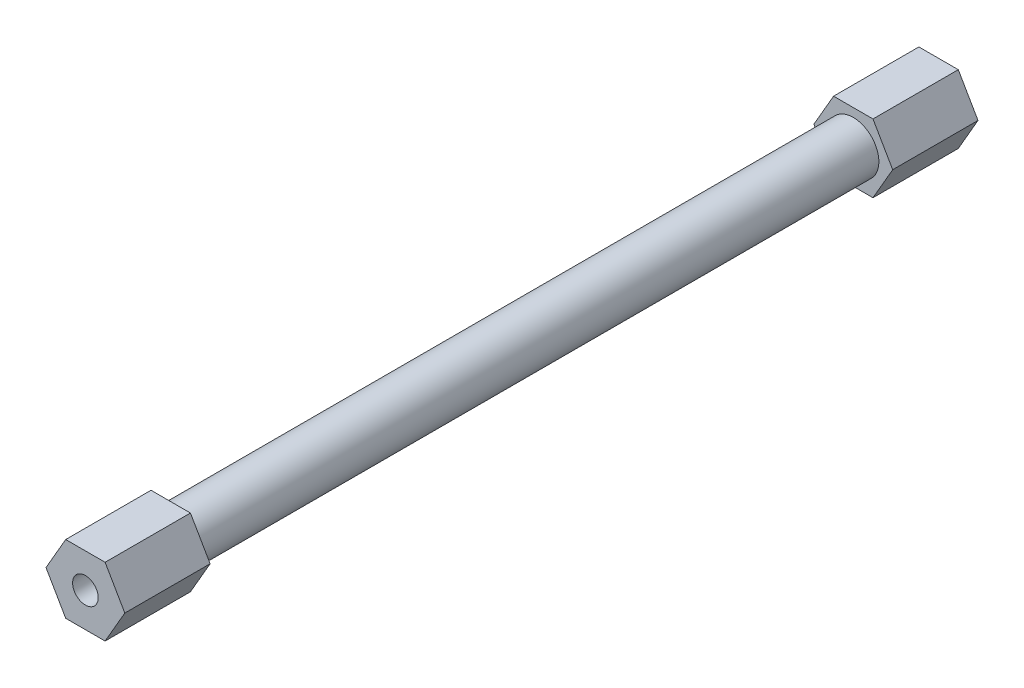
SolidWorks part; units mm, degrees
material "1060 Alloy"
ref_plane "Front Plane" through (0, 0, 0) normal (0, 0, 1) x (1, 0, 0)
ref_plane "Top Plane" through (0, 0, 0) normal (0, 1, 0) x (1, 0, 0)
ref_plane "Right Plane" through (0, 0, 0) normal (1, 0, 0) x (0, 0, -1)
sketch "Sketch1" plane through (0, 0, 0) normal (0, 0, 1) x (1, 0, 0)
  circle A0 centre (0, 0) radius 1.5
  circle A1 centre (0, 0) radius 3
  dimension "D1" = 3
  dimension "D2" = 6
extrude "Boss-Extrude1" add sketch "Sketch1" along normal blind 100
sketch "Sketch2" plane through (0, 0, 100) normal (0, 0, 1) x (1, 0, 0)
  line L1 (4.6188, 0) -> (2.3094, 4)
  line L2 (2.3094, 4) -> (-2.3094, 4)
  line L3 (-2.3094, 4) -> (-4.6188, 0)
  line L4 (-4.6188, 0) -> (-2.3094, -4)
  line L5 (-2.3094, -4) -> (2.3094, -4)
  line L6 (2.3094, -4) -> (4.6188, 0)
  circle A0 centre (0, 0) radius 4 construction
  circle A1 centre (0, 0) radius 1.5
  dimension "D1" = 8
extrude "Boss-Extrude2" add sketch "Sketch2" against normal blind 10
ref_plane "Plane1" through (0, 0, 50) normal (0, 0, 1) x (1, 0, 0)
mirror "Mirror1" about plane through (0, 0, 50) normal (0, 0, 1) of "Boss-Extrude2"
